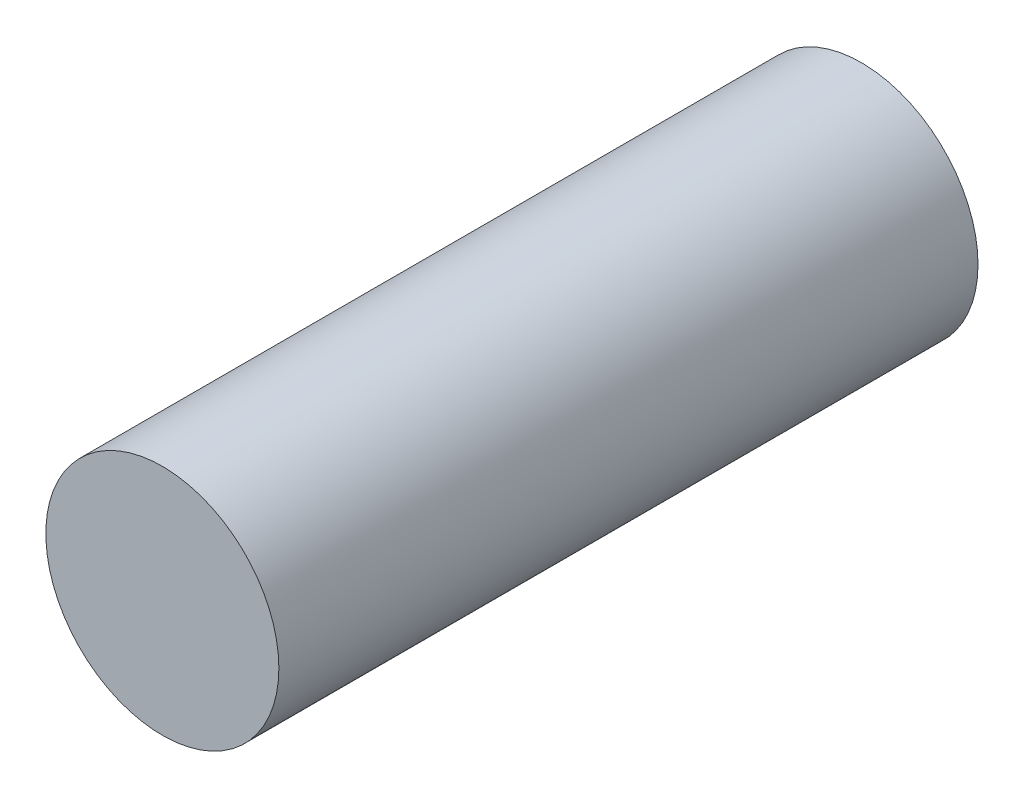
SolidWorks part; units mm, degrees
ref_plane "Front Plane" through (0, 0, 0) normal (0, 0, 1) x (1, 0, 0)
ref_plane "Top Plane" through (0, 0, 0) normal (0, 1, 0) x (1, 0, 0)
ref_plane "Right Plane" through (0, 0, 0) normal (1, 0, 0) x (0, 0, -1)
sketch "Sketch1" plane through (0, 0, 0) normal (0, 0, 1) x (1, 0, 0)
  circle A0 centre (0, 0) radius 5
  dimension "D1" = 10
extrude "Boss-Extrude1" add sketch "Sketch1" along normal blind 30 contours A0
